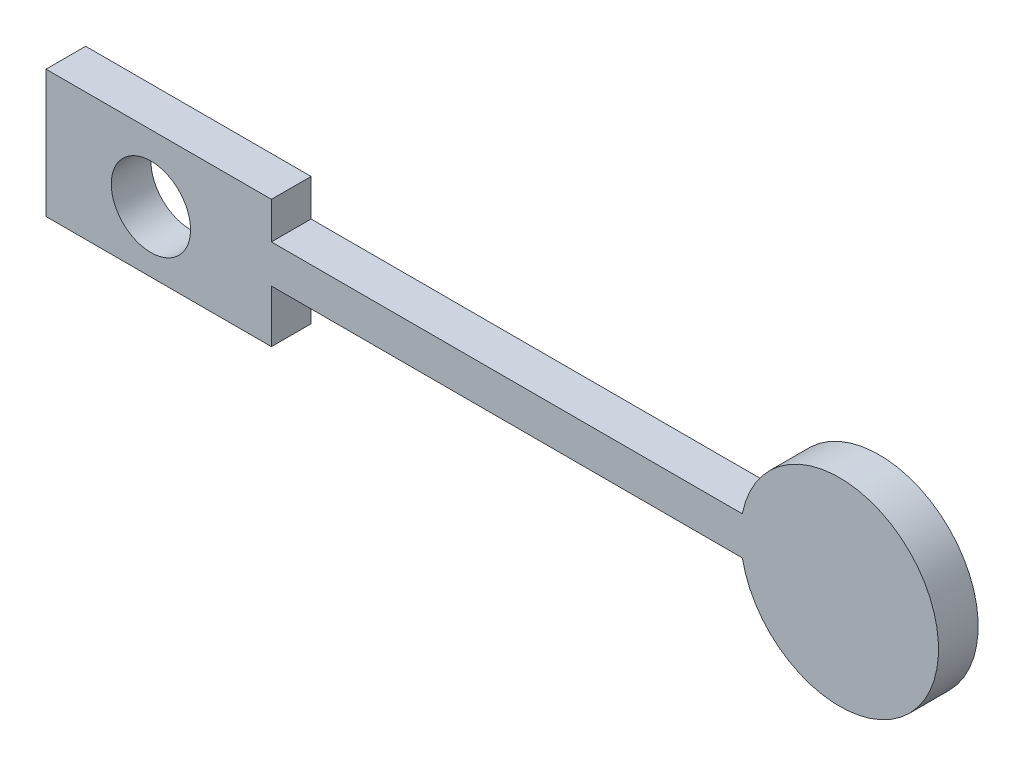
SolidWorks part; units mm, degrees
ref_plane "Front Plane" through (0, 0, 0) normal (0, 0, 1) x (1, 0, 0)
ref_plane "Top Plane" through (0, 0, 0) normal (0, 1, 0) x (1, 0, 0)
ref_plane "Right Plane" through (0, 0, 0) normal (1, 0, 0) x (0, 0, -1)
sketch "Sketch1" plane through (0, 0, 0) normal (0, 0, 1) x (1, 0, 0)
  line L0 (30.41, 7.5306) -> (30.41, 16.8403)
  line L1 (-26.4633, -15.3598) -> (30.41, -15.3598)
  line L2 (-26.4633, -15.3598) -> (-26.4633, 16.8403)
  line L3 (-26.4633, 16.8403) -> (30.41, 16.8403)
  line L4 (30.41, -15.3598) -> (30.41, -2.1083)
  line L5 (30.41, 7.5306) -> (149.2116, 7.5306)
  line L7 (30.41, -2.1083) -> (149.2116, -2.1083)
  circle A0 centre (0, 0) radius 10
  arc A1 (149.2116, -2.1083) -> (149.2116, 7.5306) centre (173.7299, 2.7112) ccw
  dimension "D1" = 20
extrude "Boss-Extrude1" add sketch "Sketch1" along normal blind 10
